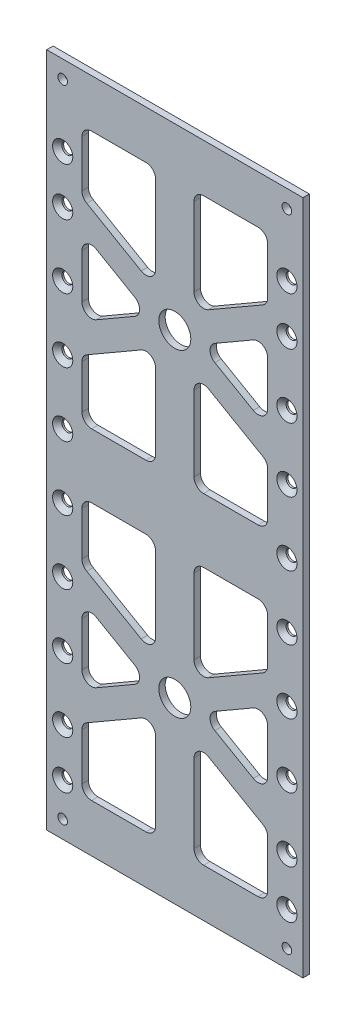
SolidWorks part; units mm, degrees
material "6061-T6 (SS)"
ref_plane "Front Plane" through (0, 0, 0) normal (0, 0, 1) x (1, 0, 0)
ref_plane "Top Plane" through (0, 0, 0) normal (0, 1, 0) x (1, 0, 0)
ref_plane "Right Plane" through (0, 0, 0) normal (1, 0, 0) x (0, 0, -1)
sketch "Sketch1" plane through (0, 0, 0) normal (0, 0, 1) x (1, 0, 0)
  line L1 (0, 0) -> (88, 0)
  line L2 (0, 0) -> (0, 211)
  line L3 (0, 211) -> (88, 211)
  line L4 (88, 0) -> (88, 211)
  dimension "D1" = 88
  dimension "D2" = 211
extrude "Boss-Extrude1" add sketch "Sketch1" along normal blind 2
sketch "Sketch2" plane through (0, 0, 2) normal (0, 0, 1) x (1, 0, 0)
  line L0 (0, 105.5) -> (88, 105.5) construction
  line L1 (0, 211) -> (0, 0) construction
  line L2 (88, 0) -> (88, 211) construction
  line L3 (44, 211) -> (44, 0) construction
  line L4 (88, 211) -> (0, 211) construction
  line L5 (0, 0) -> (88, 0) construction
  line L6 (0, 155.25) -> (88, 155.25) construction
  line L7 (0, 55.75) -> (88, 55.75) construction
  dimension "D1" = 55.75
  dimension "D2" = 55.75
sketch "Sketch3" plane through (0, 0, 2) normal (0, 0, 1) x (1, 0, 0)
  line L0 (0, 155.25) -> (88, 155.25) construction
  line L1 (38, 196) -> (38, 115.5)
  line L2 (0, 211) -> (0, 0) construction
  line L3 (15, 196) -> (73, 196)
  line L4 (15, 196) -> (15, 115.5)
  line L5 (15, 115.5) -> (73, 115.5)
  line L6 (73, 196) -> (73, 115.5)
  line L7 (88, 211) -> (0, 211) construction
  line L8 (88, 0) -> (88, 211) construction
  line L9 (0, 105.5) -> (88, 105.5) construction
  line L13 (73, 171.9932) -> (15, 138.5068) construction
  line L14 (15, 171.9932) -> (73, 138.5068) construction
  line L15 (73, 176.612) -> (15, 143.1256)
  line L16 (73, 167.3744) -> (15, 133.888)
  line L17 (15, 176.612) -> (73, 143.1256)
  line L18 (15, 167.3744) -> (73, 133.888)
  line L19 (50, 196) -> (50, 115.5)
  circle A0 centre (44, 155.25) radius 5
  dimension "D1" = 10
  dimension "D3" = 15
  dimension "D4" = 15
  dimension "D5" = 15
  dimension "D6" = 10
  dimension "D9" = 30
  dimension "D10" = 30
  dimension "D11" = 8
  dimension "D12" = 4
  dimension "D13" = 4
  dimension "D14" = 8
ref_plane "Plane1" through (0, 105.5, 0) normal (0, 1, 0) x (1, 0, 0)
extrude "Cut-Extrude2" cut sketch "Sketch3" against normal blind 2
sketch "Sketch4" plane through (0, 0, 2) normal (0, 0, 1) x (1, 0, 0)
  line L0 (0, 155.25) -> (88, 155.25) construction
  circle A0 centre (44, 155.25) radius 5
  dimension "D1" = 10
extrude "Cut-Extrude3" cut sketch "Sketch4" against normal through all
mirror "Mirror2" about plane through (0, 105.5, 0) normal (0, 1, 0) of "Cut-Extrude2", "Cut-Extrude3"
fillet "Fillet2" radius 3 44 edges at (73, 67.8744, 1) (73, 43.6256, 1) (52, 55.75, 1) (15, 15, 1) (15, 34.388, 1) (15, 143.1256, 1) (15, 167.3744, 1) (36, 155.25, 1) (15, 115.5, 1) (15, 133.888, 1) (73, 196, 1) (73, 115.5, 1) (73, 133.888, 1) (15, 196, 1) (15, 176.612, 1) (73, 167.3744, 1) (73, 143.1256, 1) (52, 155.25, 1) (73, 95.5, 1) (73, 77.112, 1) (73, 34.388, 1) (73, 15, 1) (15, 77.112, 1) (15, 95.5, 1) (15, 43.6256, 1) (15, 67.8744, 1) (36, 55.75, 1) (73, 176.612, 1) (50, 15, 1) (38, 15, 1) (38, 47.6671, 1) (50, 47.6671, 1) (38, 63.8329, 1) (38, 95.5, 1) (50, 63.8329, 1) (50, 95.5, 1) (38, 115.5, 1) (38, 147.1671, 1) (50, 147.1671, 1) (50, 115.5, 1) (38, 196, 1) (38, 163.3329, 1) (50, 163.3329, 1) (50, 196, 1)
sketch "Sketch5" plane through (0, 0, 2) normal (0, 0, 1) x (1, 0, 0)
  line L0 (0, 205.5) -> (88, 205.5) construction
  line L1 (0, 211) -> (0, 0) construction
  line L2 (88, 0) -> (88, 211) construction
  line L3 (88, 211) -> (0, 211) construction
  line L4 (79, 211) -> (79, 0) construction
  line L5 (0, 0) -> (88, 0) construction
  line L6 (9, 211) -> (9, 0) construction
  line L7 (44, 211) -> (44, 0) construction
  line L8 (0, 5.5) -> (88, 5.5) construction
  line L9 (0, 105.5) -> (88, 105.5) construction
  circle A0 centre (9, 205.5) radius 1.5
  circle A1 centre (79, 205.5) radius 1.5
  circle A2 centre (9, 5.5) radius 1.5
  circle A3 centre (79, 5.5) radius 1.5
  dimension "D5" = 3
  dimension "D1" = 200
  dimension "D2" = 70
  dimension "D3" = 35
  dimension "D4" = 100
extrude "Cut-Extrude4" cut sketch "Sketch5" against normal through all
sketch "Sketch23" plane through (0, 0, 2) normal (0, 0, 1) x (1, 0, 0)
  line L2 (88, 211) -> (88, 0)
  line L3 (86, 211) -> (86, 0)
  line L4 (86, 211) -> (88, 211)
  line L5 (86, 0) -> (88, 0)
  line L6 (2.1504, 211) -> (2.1504, 0)
  line L7 (2.1504, 211) -> (0, 211)
  line L8 (0, 211) -> (0, 0)
  line L9 (2.1504, 0) -> (0, 0)
  dimension "D1" = 2
extrude "Cut-Extrude5" cut sketch "Sketch23" against normal blind 10 contours L5 L2 L4 L3 | L6 L9 L8 L7
sketch "Sketch29" plane through (0, 0, 0) normal (0, 0, -1) x (-1, 0, 0)
  line L0 (-44, 0) -> (-44, 211)
  line L4 (-86, 105.5) -> (-2.1504, 105.5)
  line L5 (-86, 0) -> (-86, 211) construction
  line L6 (-2.1504, 0) -> (-2.1504, 211) construction
  line L16 (-4, 211) -> (1.9115, 211)
  line L17 (-4, 211) -> (-4, 0)
  line L18 (-4, 0) -> (1.9115, 0)
  line L19 (1.9115, 211) -> (1.9115, 0)
  line L20 (-84, 0) -> (-88.0365, 0)
  line L21 (-84, 0) -> (-84, 211)
  line L22 (-84, 211) -> (-88.0365, 211)
  line L23 (-88.0365, 0) -> (-88.0365, 211)
  point P0 (-44, 155.25)
  point P1 (-44, 217.1483)
  point P3 (-4, 155.25)
  point P4 (-4, 217.1483)
  point P5 (-84, 155.25)
  point P6 (-84, 217.1483)
  point P8 (-4, 105.5)
  point P22 (-84, 105.5)
  point P23 (-44, 105.5)
extrude "Cut-Extrude10" cut sketch "Sketch29" against normal blind 2
hole_wizard "CSK for M3 Flat Head Machine Screw1" positions "Sketch31" profile "Sketch32" countersink size "M3" standard "ANSI Metric"
sketch "Sketch31" plane through (0, 0, 2) normal (0, 0, 1) x (1, 0, 0)
  line L0 (44, 211) -> (44, 0) construction
  line L1 (84, 211) -> (4, 211) construction
  line L2 (4, 0) -> (84, 0) construction
  point P0 (9, 186)
  point P2 (9, 171)
  point P4 (9, 151)
  point P6 (9, 131)
  point P8 (9, 111)
  point P10 (9, 91)
  point P12 (9, 71)
  point P14 (9, 51)
  point P16 (9, 31)
  point P18 (9, 16)
  point P20 (79, 186)
  point P22 (79, 171)
  point P24 (79, 151)
  point P26 (79, 131)
  point P28 (79, 111)
  point P30 (79, 91)
  point P32 (79, 71)
  point P34 (79, 51)
  point P36 (79, 31)
  point P38 (79, 16)
  dimension "D1" = 70
  dimension "D2" = 35
  dimension "D3" = 25
  dimension "D4" = 40
  dimension "D5" = 60
  dimension "D6" = 80
  dimension "D7" = 100
  dimension "D8" = 120
  dimension "D9" = 140
  dimension "D10" = 160
  dimension "D11" = 180
  dimension "D12" = 195
sketch "Sketch32" plane through (9, 186, 2) normal (1, 0, 0) x (0, -1, 0)
  line L0 (0, 0) -> (0, 11.0215)
  line L1 (0, 11.0215) -> (1.7, 10)
  line L2 (1.7, 10) -> (1.7, 1.45)
  line L3 (1.7, 1.45) -> (3.15, 0)
  line L5 (3.15, 0) -> (0, 0)
  line L6 (-1.7, 1.45) -> (-3.15, 0) construction
  line L10 (0, 11.0215) -> (-1.7, 10) construction
  line L11 (0, -6.35) -> (0, 107.95) construction
  dimension "Hole Dia." = 3.4
  dimension "Hole Depth" = 10
  dimension "Near C'Sink Dia." = 6.3
  dimension "Near C'Sink Angle" = 90
  dimension "Drill Angle" = 118
